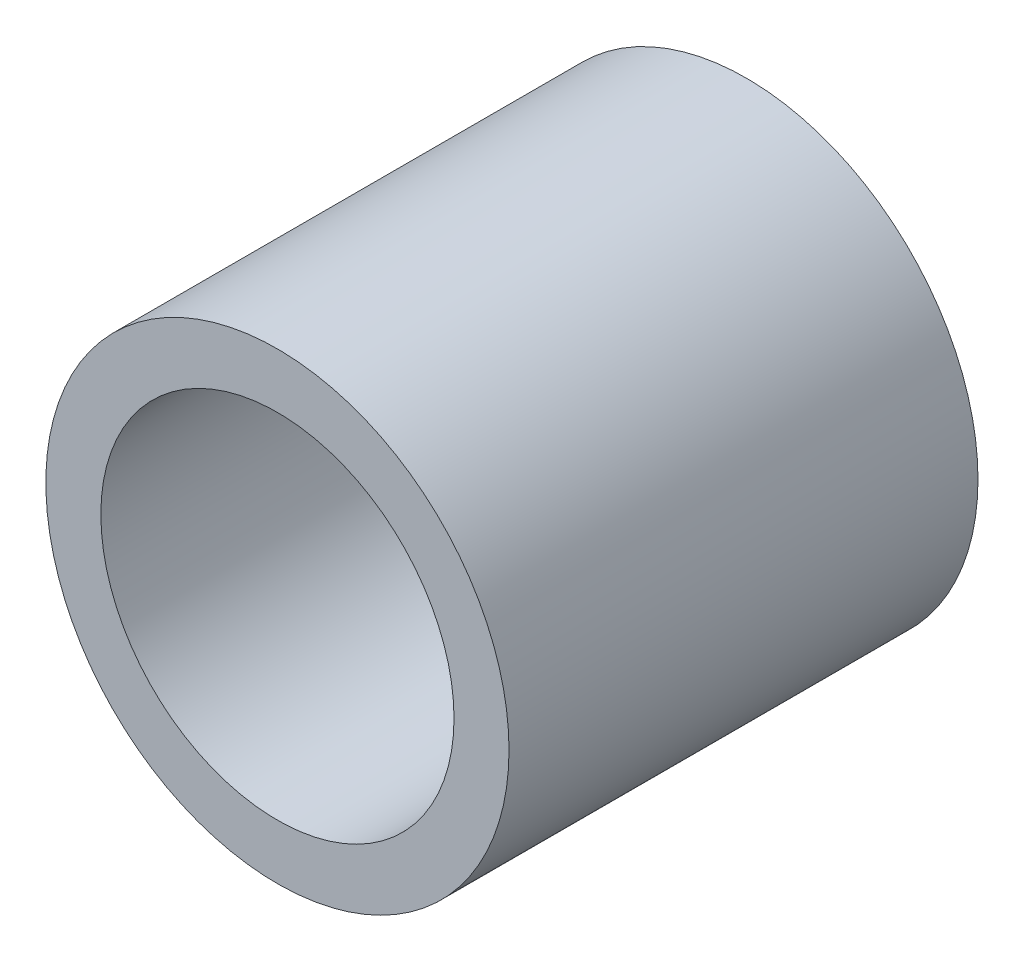
SolidWorks part; units mm, degrees
ref_plane "Front Plane" through (0, 0, 0) normal (0, 0, 1) x (1, 0, 0)
ref_plane "Top Plane" through (0, 0, 0) normal (0, 1, 0) x (1, 0, 0)
ref_plane "Right Plane" through (0, 0, 0) normal (1, 0, 0) x (0, 0, -1)
sketch "Sketch1" plane through (0, 0, 0) normal (0, 0, 1) x (1, 0, 0)
  circle A0 centre (0, -0.8124) radius 3.05
  circle A1 centre (0, -0.8124) radius 4
extrude "Boss-Extrude1" add sketch "Sketch1" along normal blind 8.1
